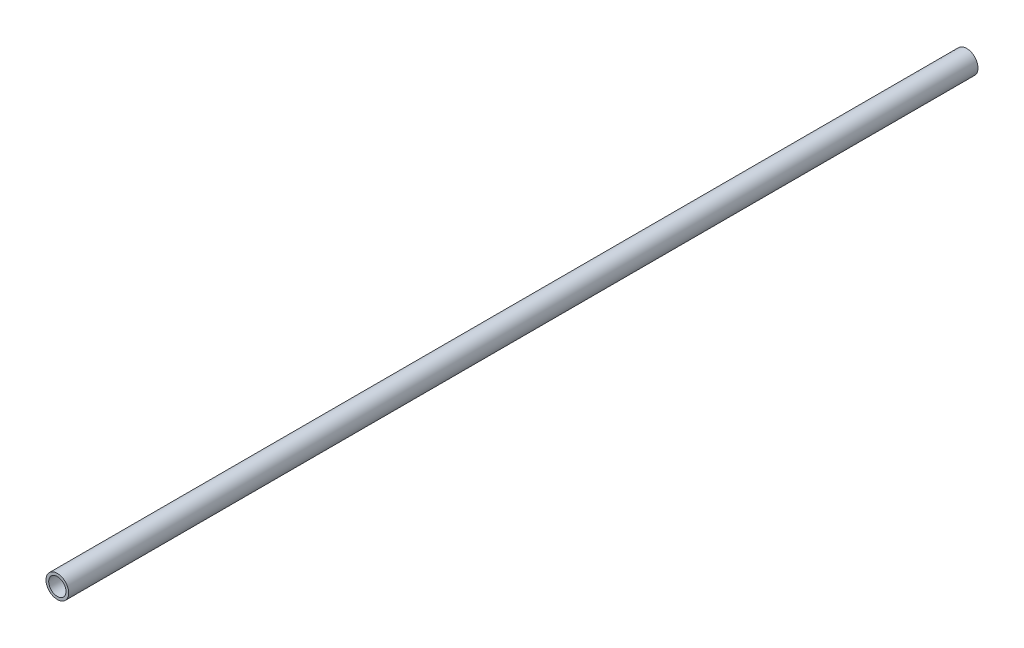
SolidWorks part; units mm, degrees
ref_plane "Plan de face" through (0, 0, 0) normal (0, 0, 1) x (1, 0, 0)
ref_plane "Plan de dessus" through (0, 0, 0) normal (0, 1, 0) x (1, 0, 0)
ref_plane "Plan de droite" through (0, 0, 0) normal (1, 0, 0) x (0, 0, -1)
sketch "Esquisse1" plane through (0, 0, 0) normal (0, 0, 1) x (1, 0, 0)
  circle A0 centre (0, 0) radius 9.5
  circle A1 centre (0, 0) radius 12.5
  dimension "D1" = 25
  dimension "D2" = 19
extrude "Boss.-Extru.2" add sketch "Esquisse1" along normal blind 1000
